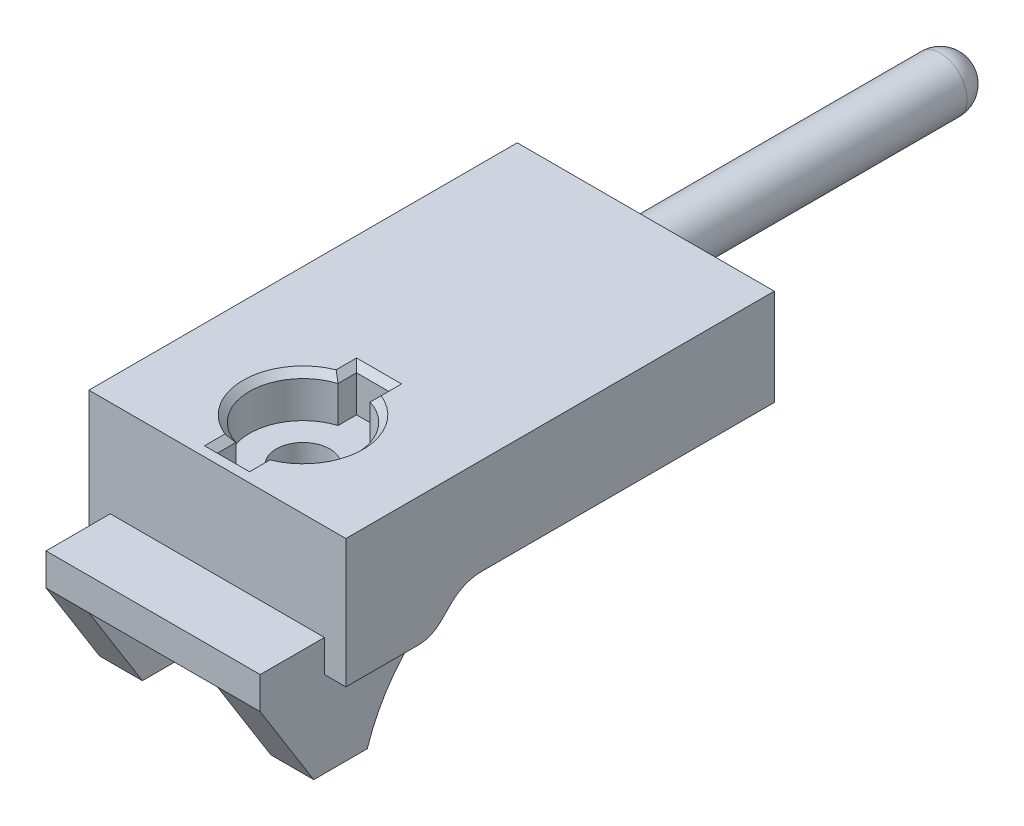
SolidWorks part; units mm, degrees
ref_plane "前视基准面" through (0, 0, 0) normal (0, 0, 1) x (1, 0, 0)
ref_plane "上视基准面" through (0, 0, 0) normal (0, 1, 0) x (1, 0, 0)
ref_plane "右视基准面" through (0, 0, 0) normal (1, 0, 0) x (0, 0, -1)
sketch "草图1" plane through (0, 0, 0) normal (0, 1, 0) x (1, 0, 0)
  line L1 (-6, 11.5) -> (6, 11.5)
  line L2 (-6, 11.5) -> (-6, -11.5)
  line L3 (-6, -11.5) -> (6, -11.5)
  line L4 (6, 11.5) -> (6, -11.5)
  line L5 (-6, 11.5) -> (6, -11.5) construction
  line L6 (-6, -11.5) -> (6, 11.5) construction
  point P0 (0, 0)
  dimension "D1" = 23
  dimension "D2" = 12
extrude "凸台-拉伸1" add sketch "草图1" along normal blind 10
sketch "草图3" plane through (0, 10, 0) normal (0, 1, 0) x (1, 0, 0)
  line L0 (6, -11.5) -> (6, 11.5) construction
  line L1 (-6, -11.5) -> (6, -11.5)
  line L2 (-6, -11.5) -> (-6, -8.5)
  line L3 (-6, -8.5) -> (6, -8.5)
  line L4 (6, -11.5) -> (6, -8.5)
  dimension "D1" = 3
extrude "切除-拉伸1" cut sketch "草图3" against normal blind 4.5
sketch "草图4" plane through (0, 0, 0) normal (0, 1, 0) x (1, 0, 0)
  line L0 (6, -8.5) -> (-6, -8.5) construction
  line L1 (6, -11.5) -> (5, -11.5)
  line L2 (6, -11.5) -> (6, -8.5)
  line L3 (6, -8.5) -> (5, -8.5)
  line L4 (5, -11.5) -> (5, -8.5)
  line L5 (6, -8.5) -> (-6, -8.5) construction
  line L6 (-6, -11.5) -> (-5, -11.5)
  line L7 (-6, -11.5) -> (-6, -8.5)
  line L8 (-6, -8.5) -> (-5, -8.5)
  line L9 (-5, -11.5) -> (-5, -8.5)
  dimension "D1" = 10
extrude "切除-拉伸2" cut sketch "草图4" along normal through all
sketch "草图5" plane through (0, 0, 0) normal (1, 0, 0) x (0, 0, -1)
  line L0 (11.5, 5.5) -> (0, 5.5)
  line L1 (11.5, 10) -> (11.5, 0) construction
  line L2 (-9, 0) -> (-11.5, 4)
  line L3 (-8.5, 10) -> (11.5, 10) construction
  line L4 (11.5, 5.5) -> (11.5, 0)
  line L5 (11.5, 0) -> (-6.5, 0)
  line L6 (-8.5, 0) -> (11.5, 0) construction
  line L7 (-11.5, 5.5) -> (-11.5, 0) construction
  line L8 (-8.5, 0) -> (-11.5, 0) construction
  line L9 (-11.5, 4) -> (-11.5, 0)
  line L10 (-11.5, 0) -> (-9, 0)
  line L11 (-8.5, 5.5) -> (-11.5, 5.5) construction
  arc A0 (0, 5.5) -> (-6.5, 0) centre (1.125, -2.4205) ccw
  dimension "D3" = 8
  dimension "D1" = 4.5
  dimension "D2" = 11.5
  dimension "D4" = 5
  dimension "D5" = 2.5
  dimension "D6" = 1.5
extrude "切除-拉伸3" cut sketch "草图5" against normal mid plane 12
sketch "草图6" plane through (6, 0, 0) normal (1, 0, 0) x (0, 0, -1)
  line L0 (-8.5, 4) -> (-4.5, 4)
  line L1 (-8.5, 0) -> (-8.5, 10) construction
  line L2 (0, 5.5) -> (-3, 5.5)
  line L3 (-3, 5.5) -> (-4.5, 4)
  line L4 (-8.5, 4) -> (-8.5, 0)
  line L5 (-8.5, 0) -> (-6.5, 0)
  line L6 (-8.5, 10) -> (11.5, 10) construction
  arc A1 (0, 5.5) -> (-6.5, 0) centre (1.125, -2.4205) ccw construction
  arc A2 (0, 5.5) -> (-6.5, 0) centre (1.125, -2.4205) ccw
  dimension "D1" = 6
  dimension "D2" = 135
  dimension "D3" = 4
extrude "切除-拉伸4" cut sketch "草图6" against normal blind 1
fillet "圆角1" radius 1.5 1 edges at (5.5, 4, 4.5)
fillet "圆角2" radius 2 1 edges at (5.5, 5.5, 3)
mirror "镜向1" about plane through (0, 0, 0) normal (1, 0, 0) of "圆角2", "圆角1", "切除-拉伸4"
sketch "草图7" plane through (0, 0, 0) normal (0, 1, 0) x (1, 0, 0)
  line L0 (-5, -11.5) -> (5, -11.5) construction
  line L1 (-3, -11.5) -> (3, -11.5)
  line L2 (-3, -11.5) -> (-3, 0)
  line L3 (-3, 0) -> (3, 0)
  line L4 (3, -11.5) -> (3, 0)
  line L5 (0, -6.5) -> (0, -13.7544) construction
  line L6 (-5, -6.5) -> (5, -6.5) construction
  line L7 (-5, 0) -> (5, 0) construction
  dimension "D1" = 6
extrude "切除-拉伸5" cut sketch "草图7" along normal up to vertex (4 mm away)
sketch "草图8" plane through (0, 0, 0) normal (0, 1, 0) x (1, 0, 0)
  line L0 (0, 11.5) -> (0, 2.7873) construction
  line L1 (4, 9.5) -> (-4, 9.5)
  line L2 (4, 9.5) -> (4, -6.5)
  line L3 (4, -6.5) -> (-4, -6.5)
  line L4 (-4, 9.5) -> (-4, -6.5)
  line L5 (-6, 11.5) -> (6, 11.5) construction
  line L6 (3, -6.5) -> (5, -6.5) construction
  dimension "D1" = 8
  dimension "D2" = 2
extrude "切除-拉伸6" cut sketch "草图8" along normal blind 8
sketch "草图9" plane through (0, 4, 0) normal (0, -1, 0) x (1, 0, 0)
  line L0 (5, 8.5) -> (-5, 8.5) construction
  line L1 (0, 0) -> (0, -6.6004) construction
  circle A0 centre (0, 4.5) radius 2.5
  dimension "D2" = 5
  dimension "D1" = 4
extrude "切除-拉伸7" cut sketch "草图9" along direction (0, -1, 0) on the side against the normal up to surface (4 mm away)
sketch "草图10" plane through (0, 8, 0) normal (0, -1, 0) x (1, 0, 0)
  line L1 (1.5, 6.5) -> (4, 6.5) construction
  line L2 (2, 1) -> (3, 2)
  line L4 (-2, 1) -> (-2, -0.5)
  line L5 (-2, -0.5) -> (2, -0.5)
  line L6 (2, -0.5) -> (2, 1)
  line L9 (-2, 1) -> (-3, 2)
  line L12 (0, 0) -> (0, -2.9413) construction
  line L13 (1.5, 6.5) -> (3, 6.5)
  line L14 (-3, 6.5) -> (-3, 2)
  line L15 (3, 6.5) -> (3, 2)
  line L16 (1.5, 6.5) -> (3, 6.5) construction
  line L17 (-4, 6.5) -> (-1.5, 6.5) construction
  line L19 (-1.5, 6.5) -> (-3, 6.5)
  arc A0 (1.5, 6.5) -> (-1.5, 6.5) centre (0, 4.5) ccw construction
  arc A1 (1.5, 6.5) -> (-1.5, 6.5) centre (0, 4.5) ccw
  dimension "D1" = 4
  dimension "D2" = 6
  dimension "D3" = 1.5
  dimension "D4" = 7
  dimension "D5" = 4.5
extrude "凸台-拉伸2" add sketch "草图10" along normal blind 2
sketch "草图11" plane through (0, 6, 0) normal (0, -1, 0) x (1, 0, 0)
  circle A0 centre (0, 4.5) radius 1.25
  arc A1 (1.5, 6.5) -> (-1.5, 6.5) centre (0, 4.5) ccw construction
  dimension "D1" = 2.5
extrude "切除-拉伸8" cut sketch "草图11" against normal through all
sketch "草图12" plane through (0, 10, 0) normal (0, 1, 0) x (1, 0, 0)
  line L0 (0, 0) -> (0, -7.0596) construction
  line L1 (0, -4.5) -> (3.3765, -4.5) construction
  line L2 (-0.75, -1.25) -> (0.75, -1.25)
  line L3 (-0.75, -1.25) -> (-0.75, -2.1152)
  line L4 (-0.75, -7.75) -> (0.75, -7.75)
  line L5 (0.75, -1.25) -> (0.75, -2.1152)
  line L6 (-0.75, -6.8848) -> (-0.75, -7.75)
  line L7 (0.75, -6.8848) -> (0.75, -7.75)
  arc A0 (-0.75, -2.1152) -> (-0.75, -6.8848) centre (0, -4.5) ccw
  circle A1 centre (0, -4.5) radius 1.25 construction
  arc A2 (0.75, -6.8848) -> (0.75, -2.1152) centre (0, -4.5) ccw
  point P11 (0, -7.75)
  dimension "D1" = 5
  dimension "D2" = 6.5
  dimension "D3" = 1.5
extrude "切除-拉伸9" cut sketch "草图12" against normal blind 2
chamfer "倒角1" distance 0.3 angle 45 8 edges at (-0.75, 10, 7.3174) (0, 10, 7.75) (0.75, 10, 7.3174) (2.5, 10, 4.5) (0.75, 10, 1.6826) (0, 10, 1.25) (-0.75, 10, 1.6826) (-2.5, 10, 4.5)
sketch "草图13" plane through (0, 0, -11.5) normal (0, 0, -1) x (-1, 0, 0)
  line L0 (0, 0) -> (0, 11.5209) construction
  line L3 (-6, 10) -> (6, 10) construction
  circle A0 centre (0, 8.5) radius 1.25
  dimension "D1" = 2.5
  dimension "D2" = 1.5
extrude "凸台-拉伸3" add sketch "草图13" along normal blind 15
fillet "圆角3" radius 1.25 1 edges at (-1.25, 8.5, -26.5)
